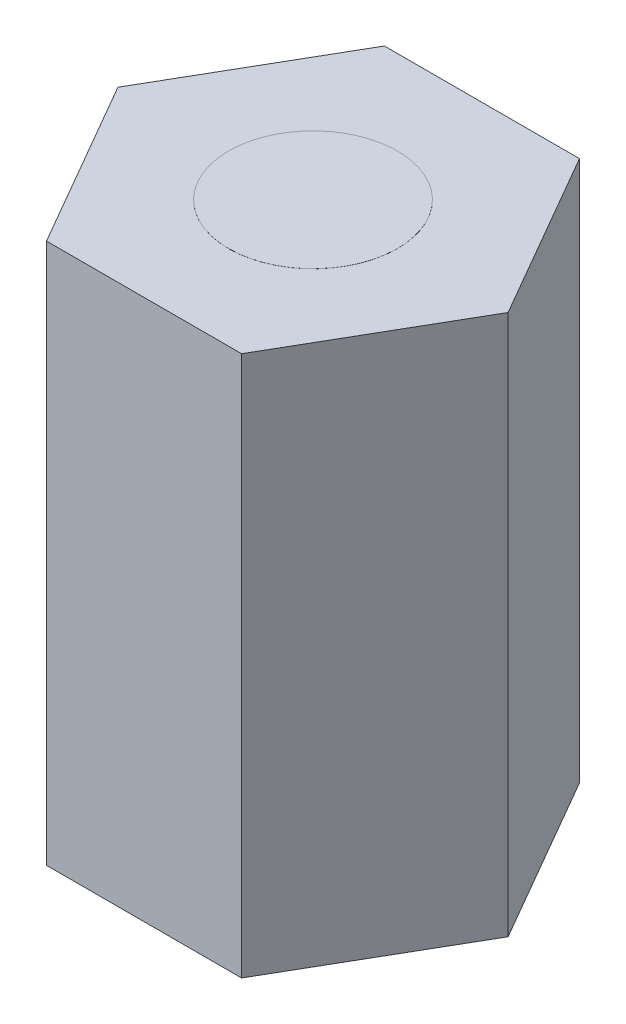
SolidWorks part; units mm, degrees
material "Brass"
ref_plane "Front Plane" through (0, 0, 0) normal (0, 0, 1) x (1, 0, 0)
ref_plane "Top Plane" through (0, 0, 0) normal (0, 1, 0) x (1, 0, 0)
ref_plane "Right Plane" through (0, 0, 0) normal (1, 0, 0) x (0, 0, -1)
sketch "Sketch1" plane through (0, 0, 0) normal (0, 1, 0) x (1, 0, 0)
  line L1 (-2.8868, 0) -> (-1.4434, -2.5)
  line L2 (-1.4434, -2.5) -> (1.4434, -2.5)
  line L3 (1.4434, -2.5) -> (2.8868, 0)
  line L4 (2.8868, 0) -> (1.4434, 2.5)
  line L5 (1.4434, 2.5) -> (-1.4434, 2.5)
  line L6 (-1.4434, 2.5) -> (-2.8868, 0)
  circle A0 centre (0, 0) radius 2.5 construction
  dimension "D1" = 5
extrude "Boss-Extrude1" add sketch "Sketch1" along normal blind 8
sketch "Sketch2" plane through (0, 8, 0) normal (0, 1, 0) x (1, 0, 0)
  circle A0 centre (0, 0) radius 1.25
  dimension "D1" = 2.5
extrude "Boss-Extrude2" add sketch "Sketch2" along normal blind 0.001
equation "\"Distance\"= 8mm"
